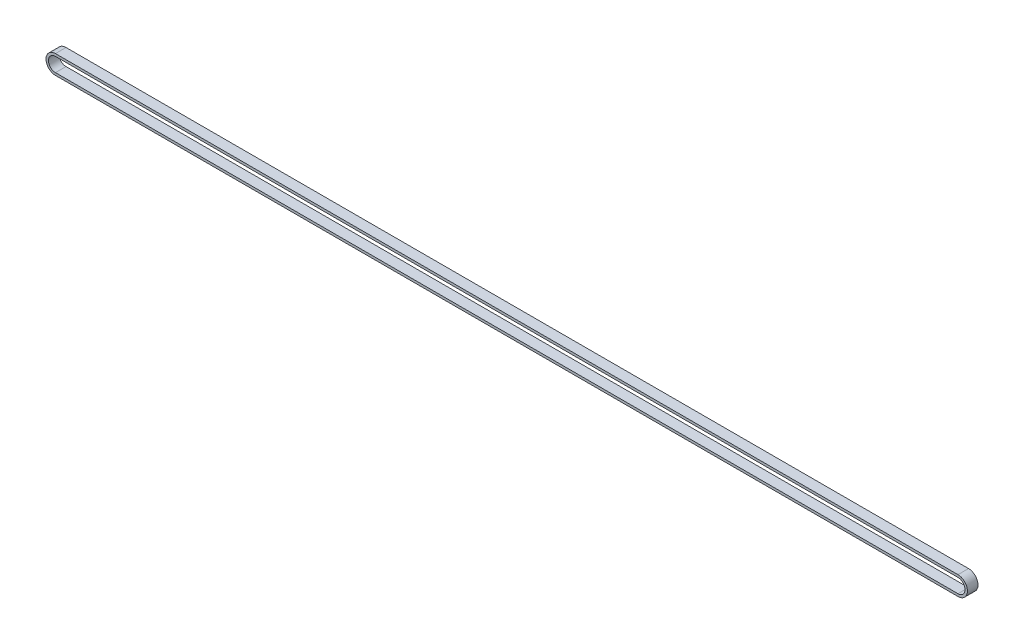
SolidWorks part; units mm, degrees
ref_plane "Front Plane" through (0, 0, 0) normal (0, 0, 1) x (1, 0, 0)
ref_plane "Top Plane" through (0, 0, 0) normal (0, 1, 0) x (1, 0, 0)
ref_plane "Right Plane" through (0, 0, 0) normal (1, 0, 0) x (0, 0, -1)
sketch "Sketch1" plane through (0, 0, 0) normal (0, 0, 1) x (1, 0, 0)
  line L0 (-256.5, 5.38) -> (256.5, 5.38)
  line L1 (-256.5, -4) -> (256.5, -4)
  line L3 (-256.5, 4) -> (256.5, 4)
  line L5 (-256.5, -4) -> (256.5, 4) construction
  line L6 (-256.5, 4) -> (256.5, -4) construction
  line L7 (-256.5, -5.38) -> (256.5, -5.38)
  arc A0 (-256.5, 4) -> (-256.5, -4) centre (-256.5, 0) ccw
  arc A1 (256.5, -4) -> (256.5, 4) centre (256.5, 0) ccw
  arc A2 (256.5, -5.38) -> (256.5, 5.38) centre (256.5, 0) ccw
  arc A3 (-256.5, 5.38) -> (-256.5, -5.38) centre (-256.5, 0) ccw
  point P0 (0, 0)
  dimension "D1" = 4
  dimension "D2" = 513
  dimension "D3" = 1.38
extrude "Boss-Extrude1" add sketch "Sketch1" along normal blind 6
